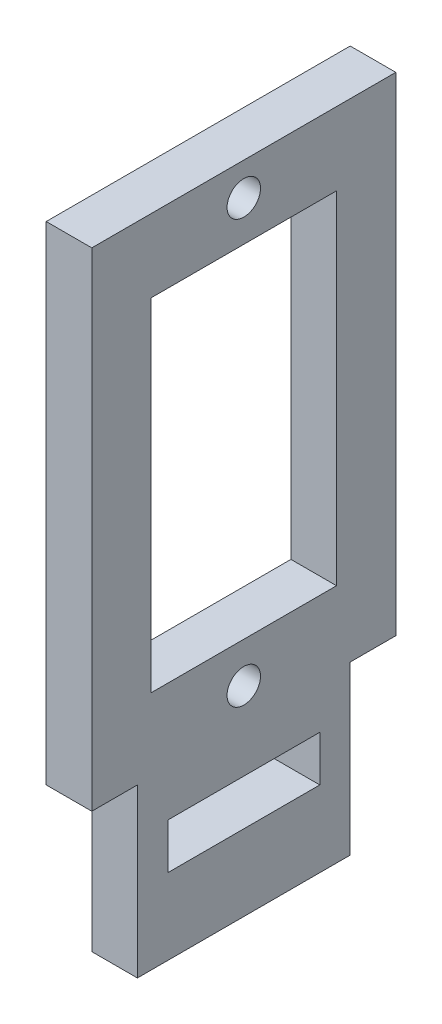
SolidWorks part; units mm, degrees
ref_plane "Front Plane" through (0, 0, 0) normal (0, 0, 1) x (1, 0, 0)
ref_plane "Top Plane" through (0, 0, 0) normal (0, 1, 0) x (1, 0, 0)
ref_plane "Right Plane" through (0, 0, 0) normal (1, 0, 0) x (0, 0, -1)
sketch "Sketch1" plane through (0, 0, 0) normal (1, 0, 0) x (0, 0, -1)
  line L0 (0, 8) -> (20, 8) construction
  line L1 (0, 0) -> (20, 0)
  line L2 (0, 0) -> (0, 43.1)
  line L3 (0, 43.1) -> (20, 43.1)
  line L4 (20, 0) -> (20, 43.1)
  line L5 (5, 8) -> (15, 8)
  line L6 (5, 5) -> (15, 5)
  line L7 (5, 5) -> (5, 8)
  line L9 (15, 5) -> (15, 8)
  point P7 (10, 8)
  dimension "D1" = 10
  dimension "D2" = 43.1
  dimension "D3" = 20
  dimension "D4" = 8
  dimension "D5" = 3
  dimension "D6" = 5
extrude "Boss-Extrude1" add sketch "Sketch1" along normal blind 3
sketch "Sketch2" plane through (0, 0, 0) normal (-1, 0, 0) x (0, 0, 1)
  line L0 (-10, 43.1) -> (-10, 40.95) construction
  line L1 (-20, 43.1) -> (0, 43.1) construction
  line L2 (-10, 40.95) -> (-10, 13.15) construction
  line L4 (-16.1, 15.8) -> (-3.9, 15.8)
  line L5 (-16.1, 15.8) -> (-16.1, 38.3)
  line L6 (-16.1, 38.3) -> (-3.9, 38.3)
  line L7 (-3.9, 15.8) -> (-3.9, 38.3)
  line L8 (-16.1, 15.8) -> (-3.9, 38.3) construction
  line L9 (-16.1, 38.3) -> (-3.9, 15.8) construction
  line L10 (-20, 0) -> (-17, 0)
  line L11 (-20, 0) -> (-20, 11)
  line L12 (-20, 11) -> (-17, 11)
  line L13 (-17, 0) -> (-17, 11)
  line L14 (0, 0) -> (-3, 0)
  line L15 (0, 0) -> (0, 11)
  line L16 (0, 11) -> (-3, 11)
  line L17 (-3, 0) -> (-3, 11)
  circle A0 centre (-10, 40.95) radius 1.1
  circle A1 centre (-10, 13.15) radius 1.1
  point P7 (-10, 27.05)
  dimension "D1" = 2.15
  dimension "D2" = 2.2
  dimension "D4" = 2.2
  dimension "D3" = 27.8
  dimension "D5" = 22.5
  dimension "D6" = 12.2
  dimension "D7" = 3
  dimension "D8" = 3
  dimension "D9" = 11
  dimension "D10" = 11
extrude "Cut-Extrude1" cut sketch "Sketch2" against normal blind 3
